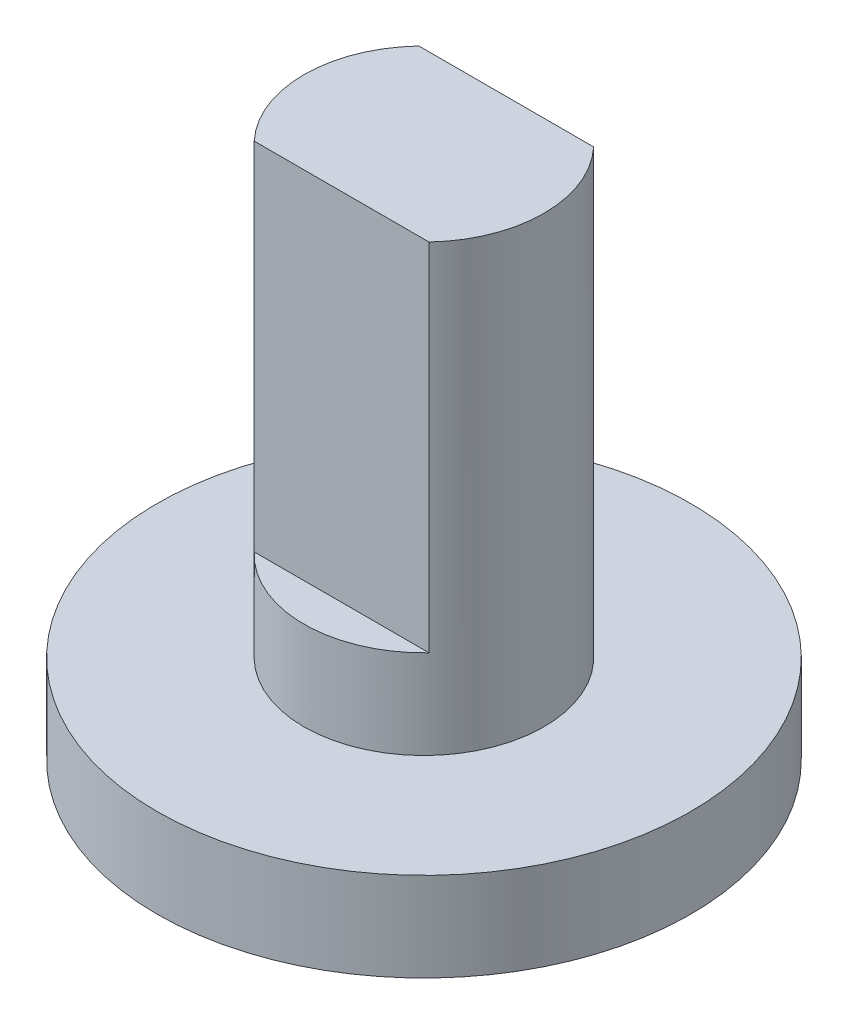
SolidWorks part; units mm, degrees
ref_plane "Front Plane" through (0, 0, 0) normal (0, 0, 1) x (1, 0, 0)
ref_plane "Top Plane" through (0, 0, 0) normal (0, 1, 0) x (1, 0, 0)
ref_plane "Right Plane" through (0, 0, 0) normal (1, 0, 0) x (0, 0, -1)
sketch "Sketch1" plane through (0, 0, 0) normal (0, 1, 0) x (1, 0, 0)
  line L0 (-1000, 0) -> (49000, 0) construction
  line L1 (0, -1000) -> (0, 49000) construction
  circle A0 centre (0, 0) radius 6
  dimension "D1" = 12
extrude "Boss-Extrude1" add sketch "Sketch1" along normal blind 2
sketch "Sketch2" plane through (0, 2, 0) normal (0, 1, 0) x (1, 0, 0)
  line L0 (-6.7193, 0) -> (6.7193, 0) construction
  line L1 (0, 6.4596) -> (0, -6.4596) construction
  circle A0 centre (0, 0) radius 2.7
  point P4 (0, 0)
  point P8 (0, 0)
  dimension "D1" = 5.4
extrude "Boss-Extrude2" add sketch "Sketch2" along normal blind 10
sketch "Sketch3" plane through (0, 12, 0) normal (0, 1, 0) x (1, 0, 0)
  line L0 (-1.965, 1.8517) -> (1.965, 1.8517)
  line L1 (-3.1067, 0) -> (3.1067, 0) construction
  line L2 (0, 4.3066) -> (0, -4.3066) construction
  line L3 (-1.965, -1.8517) -> (1.965, -1.8517)
  circle A0 centre (0, 0) radius 2.7 construction
  arc A3 (-1.965, 1.8517) -> (1.965, 1.8517) centre (0, 0) cw
  arc A4 (-1.965, -1.8517) -> (1.965, -1.8517) centre (0, 0) ccw
  point P8 (0, 0)
  point P12 (0, 0)
  dimension "D2" = 2.7
  dimension "D3" = 2.7
  dimension "D1" = 3.93
extrude "Cut-Extrude1" cut sketch "Sketch3" against normal blind 8
